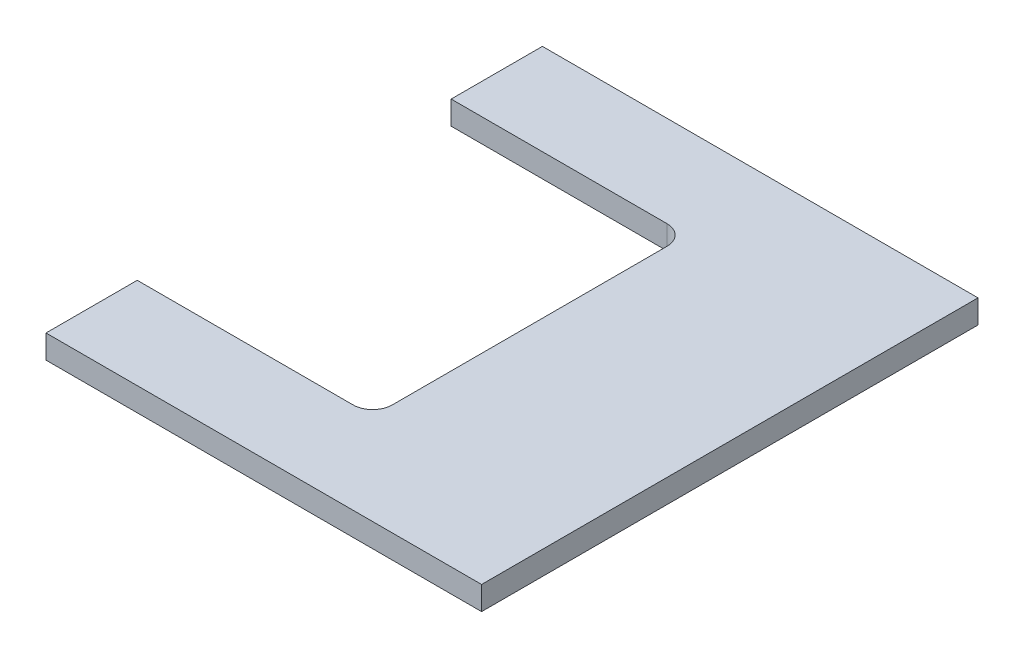
SolidWorks part; units mm, degrees
material "Acrylic (Medium-high impact)"
ref_plane "Front Plane" through (0, 0, 0) normal (0, 0, 1) x (1, 0, 0)
ref_plane "Top Plane" through (0, 0, 0) normal (0, 1, 0) x (1, 0, 0)
ref_plane "Right Plane" through (0, 0, 0) normal (1, 0, 0) x (0, 0, -1)
sketch "Sketch1" plane through (0, 0, 0) normal (0, 1, 0) x (1, 0, 0)
  line L1 (0, 0) -> (111, 0)
  line L2 (0, 0) -> (0, 126.5)
  line L3 (0, 126.5) -> (111, 126.5)
  line L4 (111, 0) -> (111, 126.5)
  dimension "D1" = 126.5
  dimension "D2" = 111
extrude "Boss-Extrude1" add sketch "Sketch1" along normal blind 6
sketch "Sketch2" plane through (0, 6, 0) normal (0, 1, 0) x (1, 0, 0)
  line L0 (0, 126.5) -> (0, 0) construction
  line L1 (0, 103.25) -> (60, 103.25)
  line L2 (0, 103.25) -> (0, 23.25)
  line L3 (0, 23.25) -> (60, 23.25)
  line L4 (60, 103.25) -> (60, 23.25)
  line L5 (111, 0) -> (111, 126.5) construction
  point P8 (111, 63.25)
  point P9 (60, 63.25)
  dimension "D1" = 80
  dimension "D2" = 60
extrude "Cut-Extrude1" cut sketch "Sketch2" against normal through all
fillet "Fillet1" radius 5 2 edges at (60, 3, -23.25) (60, 3, -103.25)
